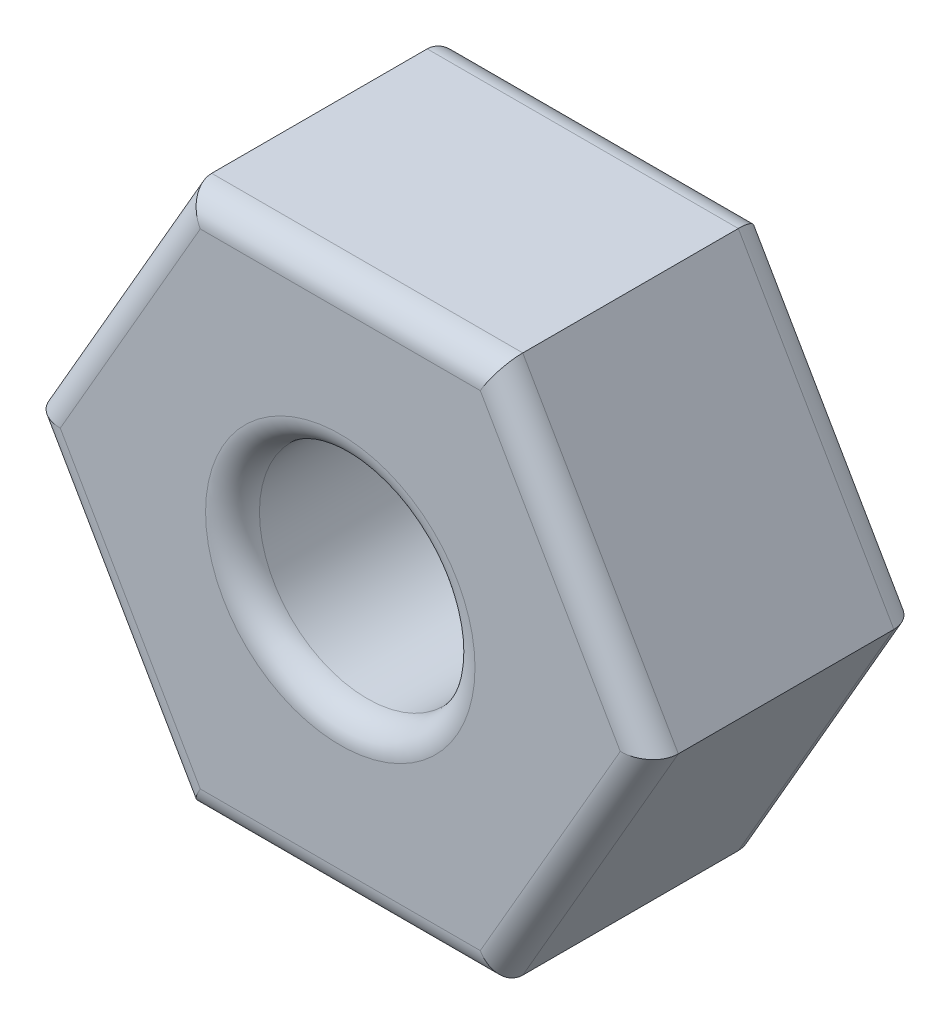
SolidWorks part; units mm, degrees
ref_plane "Front Plane" through (0, 0, 0) normal (0, 0, 1) x (1, 0, 0)
ref_plane "Top Plane" through (0, 0, 0) normal (0, 1, 0) x (1, 0, 0)
ref_plane "Right Plane" through (0, 0, 0) normal (1, 0, 0) x (0, 0, -1)
sketch "Sketch1" plane through (0, 0, 0) normal (0, 0, 1) x (1, 0, 0)
  line L1 (2.3094, 0) -> (1.1547, 2)
  line L2 (1.1547, 2) -> (-1.1547, 2)
  line L3 (-1.1547, 2) -> (-2.3094, 0)
  line L4 (-2.3094, 0) -> (-1.1547, -2)
  line L5 (-1.1547, -2) -> (1.1547, -2)
  line L6 (1.1547, -2) -> (2.3094, 0)
  circle A0 centre (0, 0) radius 2 construction
  circle A1 centre (0, 0) radius 0.8
  dimension "D1" = 4
  dimension "D2" = 1.6
extrude "Boss-Extrude1" add sketch "Sketch1" along normal blind 2
fillet "Fillet1" radius 0.2 14 edges at (0.8, 0, 2) (0, -2, 2) (-1.7321, -1, 2) (-1.7321, 1, 2) (0, 2, 2) (1.7321, 1, 2) (1.7321, -1, 2) (0.8, 0, 0) (1.7321, 1, 0) (0, 2, 0) (-1.7321, 1, 0) (-1.7321, -1, 0) (0, -2, 0) (1.7321, -1, 0)
